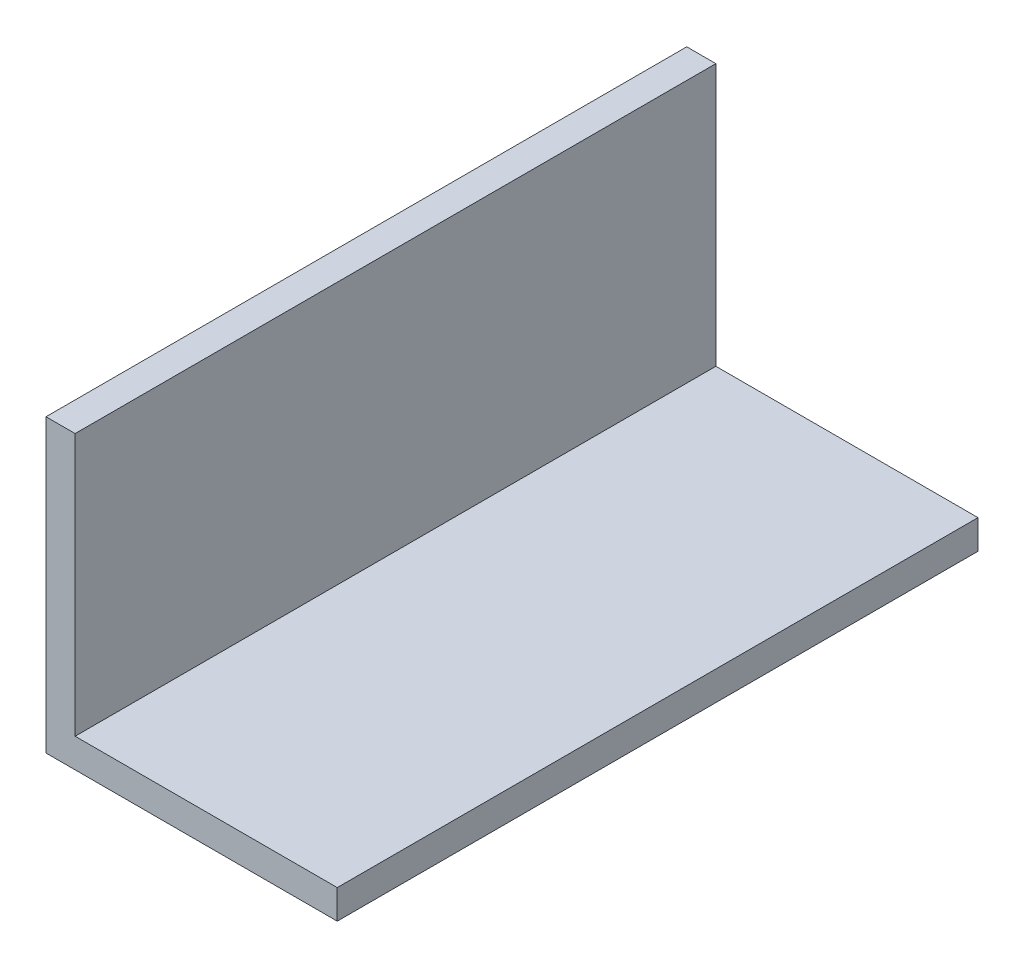
SolidWorks part; units mm, degrees
ref_plane "Спереди" through (0, 0, 0) normal (0, 0, 1) x (1, 0, 0)
ref_plane "Сверху" through (0, 0, 0) normal (0, 1, 0) x (1, 0, 0)
ref_plane "Справа" through (0, 0, 0) normal (1, 0, 0) x (0, 0, -1)
sketch "Эскиз1" plane through (0, 0, 0) normal (0, 0, 1) x (1, 0, 0)
  line L0 (0, 30) -> (0, 0)
  line L1 (0, 0) -> (30, 0)
  line L2 (0, 30) -> (3, 30)
  line L3 (3, 30) -> (3, 3)
  line L4 (3, 3) -> (30, 3)
  line L5 (30, 3) -> (30, 0)
extrude "Бобышка-Вытянуть1" add sketch "Эскиз1" along normal blind 66
